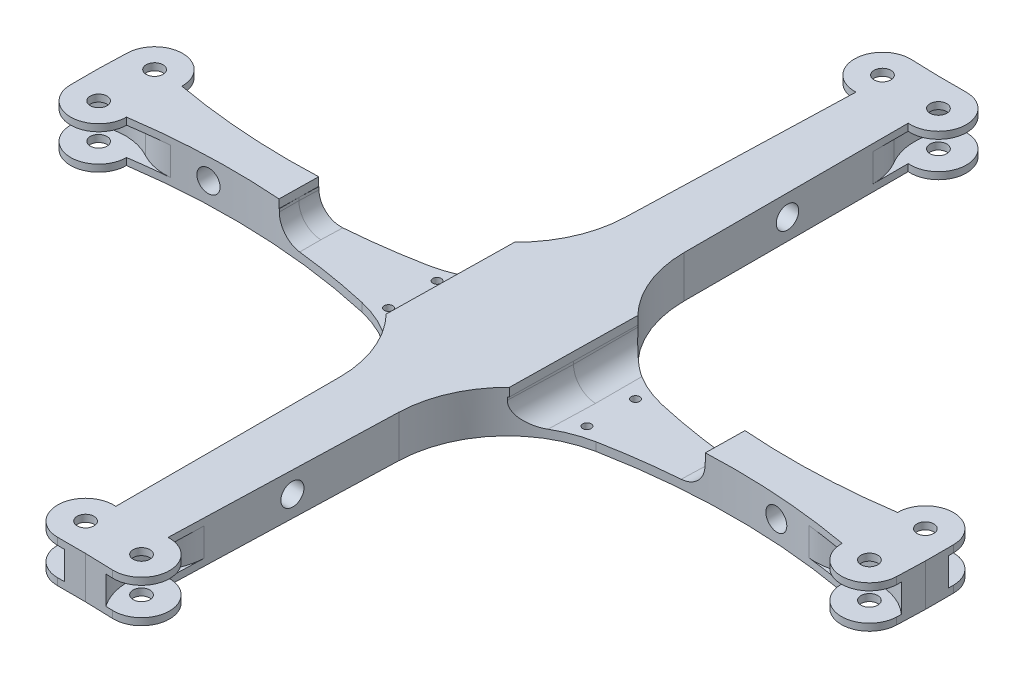
SolidWorks part; units mm, degrees
ref_plane "Front Plane" through (0, 0, 0) normal (0, 0, 1) x (1, 0, 0)
ref_plane "Top Plane" through (0, 0, 0) normal (0, 1, 0) x (1, 0, 0)
ref_plane "Right Plane" through (0, 0, 0) normal (1, 0, 0) x (0, 0, -1)
sketch "Sketch1" plane through (0, 0, 0) normal (0, 1, 0) x (1, 0, 0)
  line L2 (-100.2535, 84.6898) -> (-100.2535, 4.6547)
  line L4 (38.2333, -37.6602) -> (38.2333, -47.6602)
  line L5 (-109.4156, 104.6547) -> (-99.4156, 104.6547)
  line L6 (-111.7486, -45.3272) -> (38.2333, -47.6602)
  line L7 (-111.7486, -45.3272) -> (-109.4156, 104.6547)
  arc A0 (-100.2535, 4.6547) -> (-69.0675, -34.3622) centre (-60.2535, 4.6547) ccw
  arc A1 (-99.4156, 104.6547) -> (-100.2535, 84.6898) centre (-99.4156, 94.6547) cw
  arc A4 (38.2333, -37.6602) -> (18.2333, -37.6216) centre (28.2333, -37.6602) ccw
  circle A5 centre (-99.4156, 94.6547) radius 3
  circle A6 centre (28.2333, -37.6602) radius 3
  arc A7 (-69.0675, -34.3622) -> (18.2333, -37.6216) centre (-16.7015, 197.4482) ccw
  dimension "D5" = 40
  dimension "D6" = 10
  dimension "D7" = 90
  dimension "D9" = 10
  dimension "D10" = 6
  dimension "D11" = 6
  dimension "D1" = 150
  dimension "D2" = 150
  dimension "D3" = 10
  dimension "D4" = 10
extrude "Boss-Extrude1" add sketch "Sketch1" along normal mid plane 15
sketch "Sketch2" plane through (0, 0, 0) normal (0, 0, 1) x (1, 0, 0)
  line L1 (-34.4156, -4.5) -> (-89.4156, -4.5)
  line L2 (-34.4156, -4.5) -> (-34.4156, 4.5)
  line L3 (-34.4156, 4.5) -> (-89.4156, 4.5)
  line L4 (-89.4156, -4.5) -> (-89.4156, 4.5)
  line L5 (-34.4156, -4.5) -> (-89.4156, 4.5) construction
  line L6 (-34.4156, 4.5) -> (-89.4156, -4.5) construction
  point P0 (-61.9156, 0)
  dimension "D1" = 55
  dimension "D2" = 4.5
  dimension "D4" = 34.4156
extrude "Cut-Extrude1" cut sketch "Sketch2" along normal through all
ref_plane "Plane1" through (25.2333, 0, 0) normal (1, 0, 0) x (0, 0, -1)
sketch "Sketch3" plane through (25.2333, 0, 0) normal (1, 0, 0) x (0, 0, -1)
  line L0 (-37.6602, 7.5) -> (-37.6602, -7.5) construction
  line L1 (-24.1602, -5) -> (-44.1602, -5)
  line L2 (-24.1602, -5) -> (-24.1602, 5)
  line L3 (-24.1602, 5) -> (-44.1602, 5)
  line L4 (-44.1602, -5) -> (-44.1602, 5)
  line L5 (-24.1602, -5) -> (-44.1602, 5) construction
  line L6 (-24.1602, 5) -> (-44.1602, -5) construction
  point P0 (-34.1602, 0)
  dimension "D1" = 10
  dimension "D2" = 20
  dimension "D3" = 3.5
revolve "Cut-Revolve1" cut sketch "Sketch3" angle 360 about L2
ref_plane "Plane2" through (0, 0, -92.6547) normal (0, 0, -1) x (-1, 0, 0)
sketch "Sketch4" plane through (0, 0, -92.6547) normal (0, 0, -1) x (-1, 0, 0)
  line L0 (99.4156, 7.5) -> (99.4156, -7.5) construction
  line L1 (85.9156, 5) -> (105.9156, 5)
  line L2 (85.9156, 5) -> (85.9156, -5)
  line L3 (85.9156, -5) -> (105.9156, -5)
  line L4 (105.9156, 5) -> (105.9156, -5)
  line L5 (85.9156, 5) -> (105.9156, -5) construction
  line L6 (85.9156, -5) -> (105.9156, 5) construction
  line L7 (109.4156, 7.5) -> (109.4156, -7.5) construction
  point P0 (95.9156, 0)
  point P10 (109.4156, 0)
  dimension "D1" = 10
  dimension "D2" = 20
  dimension "D3" = 3.5
revolve "Cut-Revolve2" cut sketch "Sketch4" angle 360 about L2
fillet "Fillet1" radius 20 1 edges at (-100.2535, 0, -78.7111)
fillet "Fillet2" radius 20 1 edges at (11.3366, 0, 38.5436)
sketch "Sketch6" plane through (0, 7.5, 0) normal (0, 1, 0) x (1, 0, 0)
  circle A0 centre (-75.6198, -37.3453) radius 1.5
  dimension "D1" = 3
  dimension "D2" = 37
  dimension "D3" = 42
extrude "Cut-Extrude3" cut sketch "Sketch6" against normal through all
sketch "Sketch7" plane through (-0.7319, 0, 47.0541) normal (-0.0156, 0, 0.9999) x (0.9999, 0, 0.0156)
  circle A0 centre (-8, 0) radius 4
  dimension "D1" = 8
  dimension "D2" = 8
extrude "Cut-Extrude4" cut sketch "Sketch7" against normal blind 10
sketch "Sketch8" plane through (-111.0166, 0, -1.7269) normal (-0.9999, 0, -0.0156) x (-0.0156, 0, 0.9999)
  circle A0 centre (-40, 0) radius 4
  dimension "D1" = 8
  dimension "D2" = 40
extrude "Cut-Extrude5" cut sketch "Sketch8" against normal through all
sketch "Sketch9" plane through (-0.7319, 0, 47.0541) normal (-0.0156, 0, 0.9999) x (0.9999, 0, 0.0156)
  line L0 (-88.6944, 4.5) -> (-88.6944, -4.5) construction
  line L1 (-88.6944, 4.5) -> (-33.6877, 4.5)
  line L2 (-88.6944, 4.5) -> (-88.6944, 8.8541)
  line L3 (-88.6944, 8.8541) -> (-33.6877, 8.8541)
  line L4 (-33.6877, 4.5) -> (-33.6877, 8.8541)
  line L5 (-33.6877, -4.5) -> (-33.6877, 4.5) construction
extrude "Cut-Extrude6" cut sketch "Sketch9" against normal through all
fillet "Fillet3" radius 8 2 edges at (-34.4156, -4.5, 43.0362) (-89.4156, -4.5, 34.1992)
mirror "Mirror1" about plane through (-111.7486, 7.5, 45.3272) normal (0.9999, 0, 0.0156) of bodies 109
mirror "Mirror2" about plane through (-111.7486, 7.5, 45.3272) normal (0.0156, 0, -0.9999) of bodies 110
